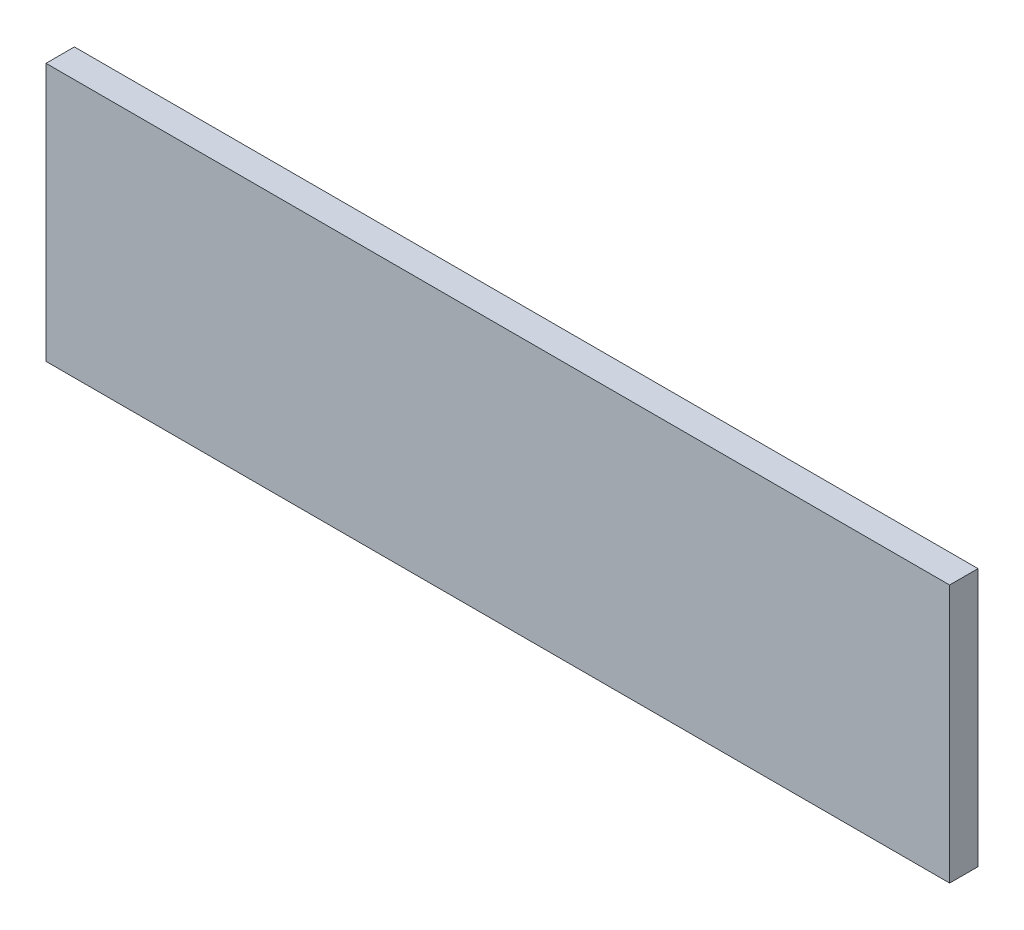
SolidWorks part; units mm, degrees
ref_plane "Front Plane" through (0, 0, 0) normal (0, 0, 1) x (1, 0, 0)
ref_plane "Top Plane" through (0, 0, 0) normal (0, 1, 0) x (1, 0, 0)
ref_plane "Right Plane" through (0, 0, 0) normal (1, 0, 0) x (0, 0, -1)
sketch "Sketch2" plane through (0, 0, 0) normal (0, 0, 1) x (1, 0, 0)
  line L1 (-134.4, 59.2667) -> (215.6, 59.2667)
  line L2 (-134.4, 59.2667) -> (-134.4, -40.7333)
  line L3 (-134.4, -40.7333) -> (215.6, -40.7333)
  line L4 (215.6, 59.2667) -> (215.6, -40.7333)
  dimension "D1" = 350
  dimension "D2" = 100
extrude "Boss-Extrude1" add sketch "Sketch2" along normal blind 11
